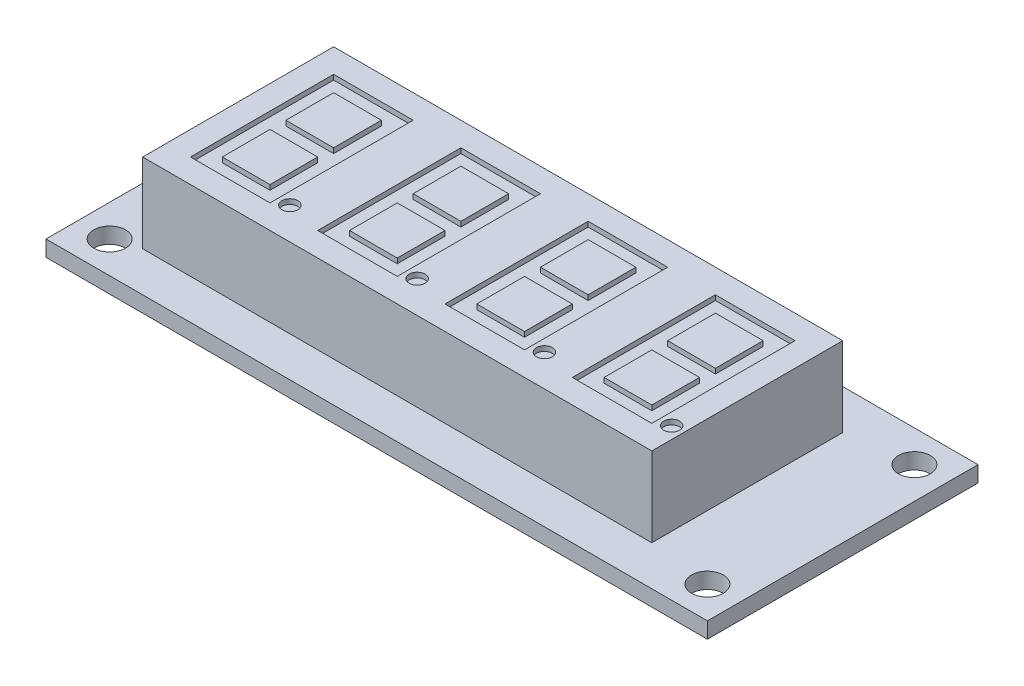
SolidWorks part; units mm, degrees
ref_plane "Front Plane" through (0, 0, 0) normal (0, 0, 1) x (1, 0, 0)
ref_plane "Top Plane" through (0, 0, 0) normal (0, 1, 0) x (1, 0, 0)
ref_plane "Right Plane" through (0, 0, 0) normal (1, 0, 0) x (0, 0, -1)
sketch "Sketch1" plane through (0, 0, 0) normal (0, 1, 0) x (1, 0, 0)
  line L1 (0, 0) -> (66, 0)
  line L2 (0, 0) -> (0, 27)
  line L3 (0, 27) -> (66, 27)
  line L4 (66, 0) -> (66, 27)
  line L5 (3.175, 3.175) -> (62.825, 3.175) construction
  line L6 (3.175, 3.175) -> (3.175, 23.825) construction
  line L7 (3.175, 23.825) -> (62.825, 23.825) construction
  line L8 (62.825, 3.175) -> (62.825, 23.825) construction
  line L9 (66, 0) -> (62.825, 0) construction
  line L10 (3.175, 23.825) -> (0, 23.825) construction
  line L11 (3.175, 23.825) -> (3.175, 27) construction
  line L12 (3.175, 27) -> (0, 27) construction
  line L13 (0, 23.825) -> (0, 27) construction
  line L14 (66, 0) -> (66, 3.175) construction
  line L15 (66, 3.175) -> (62.825, 3.175) construction
  line L16 (62.825, 0) -> (62.825, 3.175) construction
  circle A0 centre (62.825, 23.825) radius 1.5875
  circle A1 centre (3.175, 23.825) radius 1.5875
  circle A2 centre (3.175, 3.175) radius 1.5875
  circle A3 centre (62.825, 3.175) radius 1.5875
  dimension "D1" = 3.175
  dimension "D2" = 66
  dimension "D3" = 27
  dimension "D4" = 3.175
extrude "Boss-Extrude1" add sketch "Sketch1" along normal blind 1.5875
sketch "Sketch2" plane through (0, 1.5875, 0) normal (0, 1, 0) x (1, 0, 0)
  line L1 (5.675, 3.975) -> (56.475, 3.975)
  line L2 (5.675, 3.975) -> (5.675, 23.025)
  line L3 (5.675, 23.025) -> (56.475, 23.025)
  line L4 (56.475, 3.975) -> (56.475, 23.025)
  line L6 (5.675, 23.025) -> (5.675, 27) construction
  line L7 (5.675, 27) -> (0, 27) construction
  line L8 (0, 23.025) -> (0, 27) construction
  line L9 (66, 0) -> (56.475, 0) construction
  line L10 (66, 0) -> (66, 3.975) construction
  line L11 (66, 3.975) -> (56.475, 3.975) construction
  line L12 (56.475, 0) -> (56.475, 3.975) construction
  line L13 (66, 0) -> (66, 27) construction
  dimension "D1" = 50.8
  dimension "D2" = 19.05
  dimension "D3" = 9.525
extrude "Boss-Extrude2" add sketch "Sketch2" along normal blind 7.9375
sketch "Sketch3" plane through (0, 9.525, 0) normal (0, 1, 0) x (1, 0, 0)
  line L6 (8.0563, 20.6438) -> (8.0563, 6.3563)
  line L7 (8.0563, 6.3563) -> (15.9938, 6.3563)
  line L8 (15.9938, 6.3563) -> (15.9938, 20.6438)
  line L9 (5.675, 23.025) -> (5.675, 3.975) construction
  line L10 (15.9938, 20.6438) -> (8.0563, 20.6438)
  line L11 (9.6438, 12.7062) -> (9.6438, 14.2937) construction
  line L12 (9.6438, 19.0562) -> (14.4063, 19.0562)
  line L13 (9.6438, 19.0562) -> (9.6438, 14.2937)
  line L14 (9.6438, 14.2937) -> (14.4063, 14.2937)
  line L15 (14.4063, 19.0562) -> (14.4063, 14.2937)
  line L16 (9.6438, 12.7062) -> (14.4063, 12.7062)
  line L17 (9.6438, 12.7062) -> (9.6438, 7.9437)
  line L18 (9.6438, 7.9437) -> (14.4063, 7.9437)
  line L19 (14.4063, 12.7062) -> (14.4063, 7.9437)
  line L20 (9.6438, 19.0562) -> (8.0563, 19.0562) construction
  line L21 (9.6438, 19.0562) -> (9.6438, 20.6437) construction
  line L22 (9.6438, 20.6437) -> (8.0563, 20.6438) construction
  line L23 (8.0563, 19.0562) -> (8.0563, 20.6438) construction
  line L24 (14.4063, 7.9437) -> (15.9938, 7.9437) construction
  line L25 (14.4063, 7.9437) -> (14.4063, 6.3562) construction
  line L26 (14.4063, 6.3562) -> (15.9938, 6.3563) construction
  line L27 (15.9938, 7.9437) -> (15.9938, 6.3563) construction
  line L28 (17.1844, 7.15) -> (14.4063, 7.15) construction
  line L30 (5.675, 3.975) -> (18.375, 3.975) construction
  circle A0 centre (17.1844, 7.15) radius 0.7937
  point P11 (5.675, 13.5)
  point P15 (12.025, 19.0562)
  point P16 (12.025, 20.6438)
  point P24 (8.0563, 13.5)
  point P26 (12.025, 3.975)
  point P27 (12.025, 6.3562)
  dimension "D4" = 1.5875
  dimension "D1" = 14.2875
  dimension "D2" = 1.5875
  dimension "D3" = 12.7
  dimension "D5" = 2.7781
extrude "Cut-Extrude1" cut sketch "Sketch3" against normal blind 0.5
pattern_linear "LPattern1" count 4 spacing 12.7 along (1, 0, 0) of "Cut-Extrude1"
